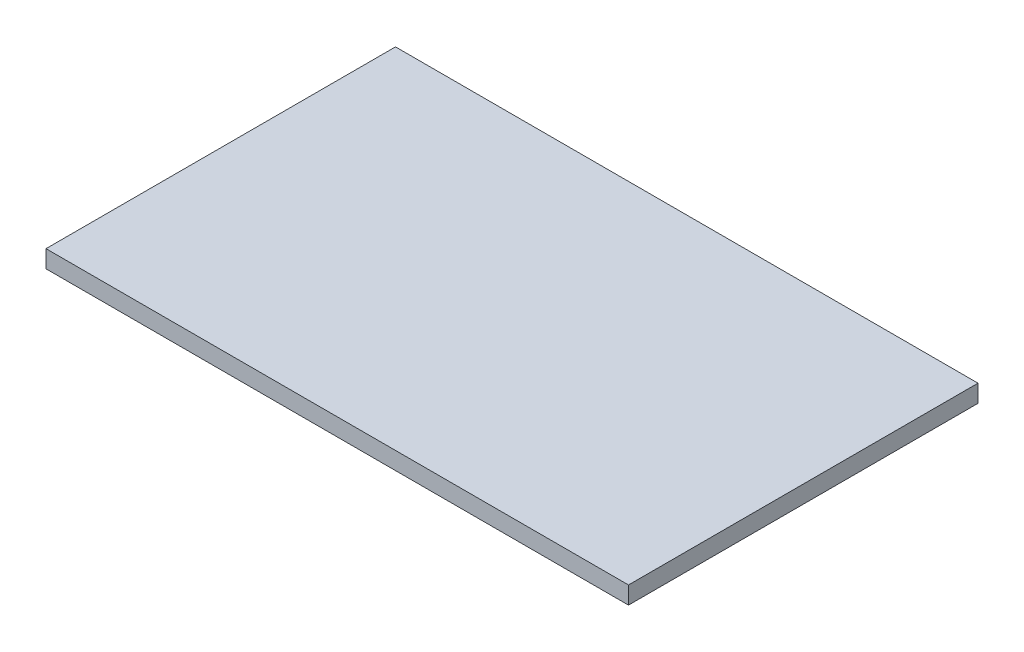
SolidWorks part; units mm, degrees
ref_plane "Front" through (0, 0, 0) normal (0, 0, 1) x (1, 0, 0)
ref_plane "Top" through (0, 0, 0) normal (0, 1, 0) x (1, 0, 0)
ref_plane "Right" through (0, 0, 0) normal (1, 0, 0) x (0, 0, -1)
sketch "Sketch1" plane through (0, 0, 0) normal (0, 1, 0) x (1, 0, 0)
  line L1 (0, 0) -> (10, 0)
  line L2 (0, 0) -> (0, 6)
  line L3 (0, 6) -> (10, 6)
  line L4 (10, 0) -> (10, 6)
  dimension "D1" = 10
  dimension "D2" = 6
extrude "Boss-Extrude1" add sketch "Sketch1" along normal blind 0.3
